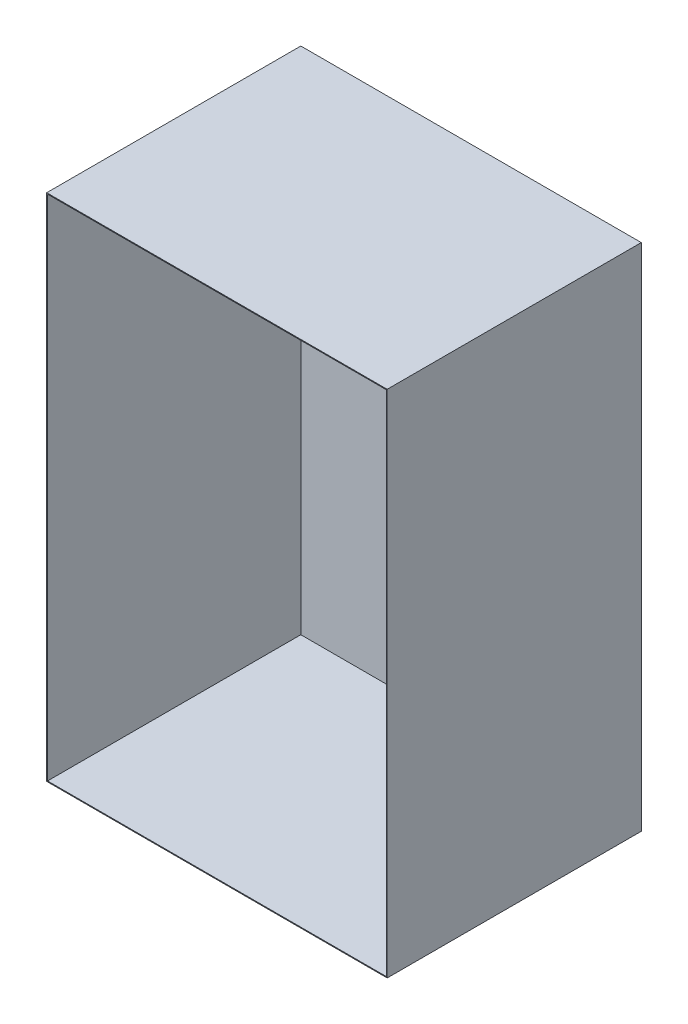
SolidWorks part; units mm, degrees
ref_plane "Front Plane" through (0, 0, 0) normal (0, 0, 1) x (1, 0, 0)
ref_plane "Top Plane" through (0, 0, 0) normal (0, 1, 0) x (1, 0, 0)
ref_plane "Right Plane" through (0, 0, 0) normal (1, 0, 0) x (0, 0, -1)
sketch "Sketch1" plane through (0, 0, 0) normal (0, 0, 1) x (1, 0, 0)
  line L8 (-201, 301) -> (201, 301)
  line L9 (-200, 300) -> (200, 300)
  line L10 (-201, 301) -> (-201, -301)
  line L11 (-201, -301) -> (201, -301)
  line L12 (201, -301) -> (201, 301)
  line L13 (200, -300) -> (200, 300)
  line L14 (-200, -300) -> (200, -300)
  line L15 (-200, 300) -> (-200, -300)
  dimension "D1" = 1
extrude "Boss-Extrude1" add sketch "Sketch1" along normal blind 299
sketch "Sketch2" plane through (0, 0, 0) normal (0, 0, -1) x (-1, 0, 0)
  line L0 (-201, 301) -> (-201, -301)
  line L1 (-201, -301) -> (201, -301)
  line L2 (201, -301) -> (201, 301)
  line L3 (201, 301) -> (-201, 301)
extrude "Boss-Extrude2" add sketch "Sketch2" along normal blind 1
